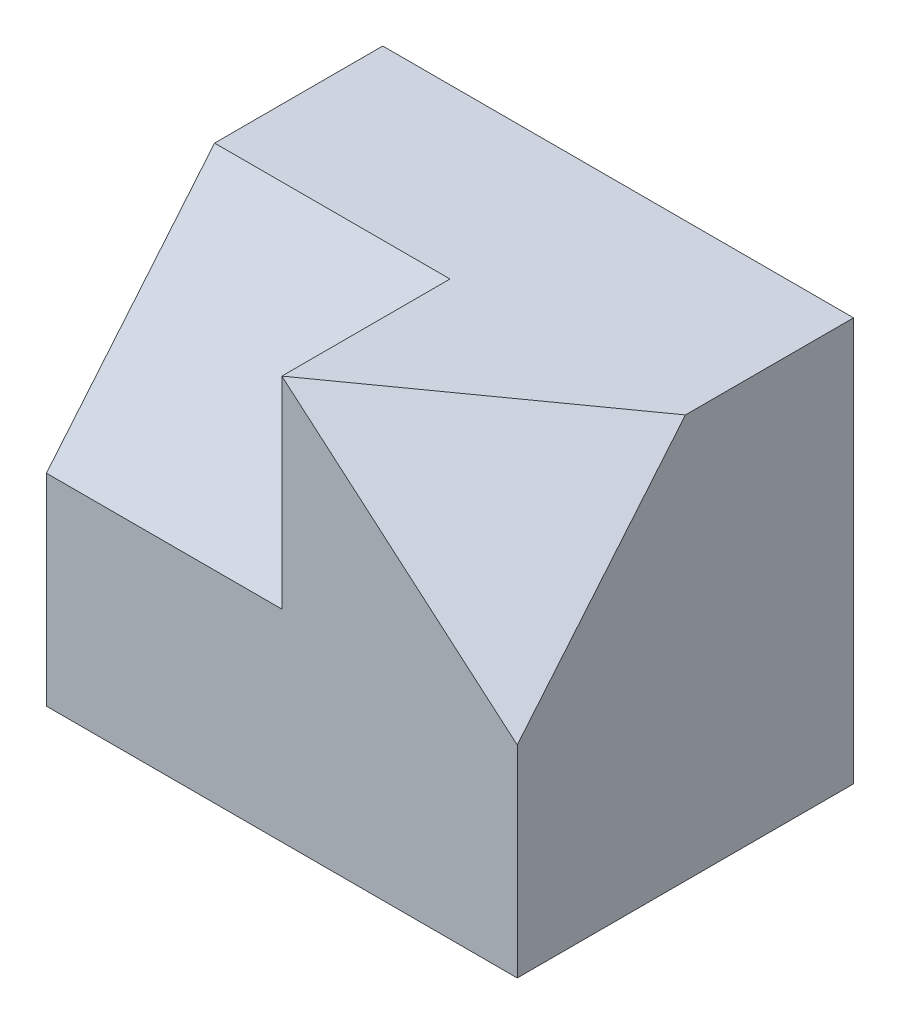
SolidWorks part; units mm, degrees
ref_plane "Plano frontal" through (0, 0, 0) normal (0, 0, 1) x (1, 0, 0)
ref_plane "Plano superior" through (0, 0, 0) normal (0, 1, 0) x (1, 0, 0)
ref_plane "Plano direito" through (0, 0, 0) normal (1, 0, 0) x (0, 0, -1)
sketch "Esboço1" plane through (0, 0, 0) normal (0, 1, 0) x (1, 0, 0)
  line L0 (0, 0) -> (0, -25) construction
  line L1 (-35, 25) -> (35, 25)
  line L2 (-35, 25) -> (-35, -25)
  line L3 (-35, -25) -> (35, -25)
  line L4 (35, 25) -> (35, -25)
  line L5 (0, 0) -> (35, 0) construction
  dimension "D1" = 70
  dimension "D2" = 50
extrude "Extrusão1" add sketch "Esboço1" along normal blind 60
sketch "Esboço5" plane through (-35, 0, 0) normal (-1, 0, 0) x (0, 0, 1)
  line L0 (0, 60) -> (25, 30)
  line L1 (-25, 60) -> (25, 60) construction
  line L2 (25, 60) -> (25, 0) construction
  line L3 (25, 60) -> (25, 30)
  line L4 (0, 60) -> (25, 60)
extrude "Corte-extrusão2" cut sketch "Esboço5" against normal blind 35
sketch "Esboço7" plane through (0, 60, 0) normal (0, 1, 0) x (1, 0, 0)
  line L0 (0, -25) -> (35, 0)
ref_plane "Plano3" through (24.2993, 28.3492, 34.019) normal (-0.4811, -0.5612, -0.6735) x (-0.8767, 0.308, 0.3696)
other "Corte de superfície4"
